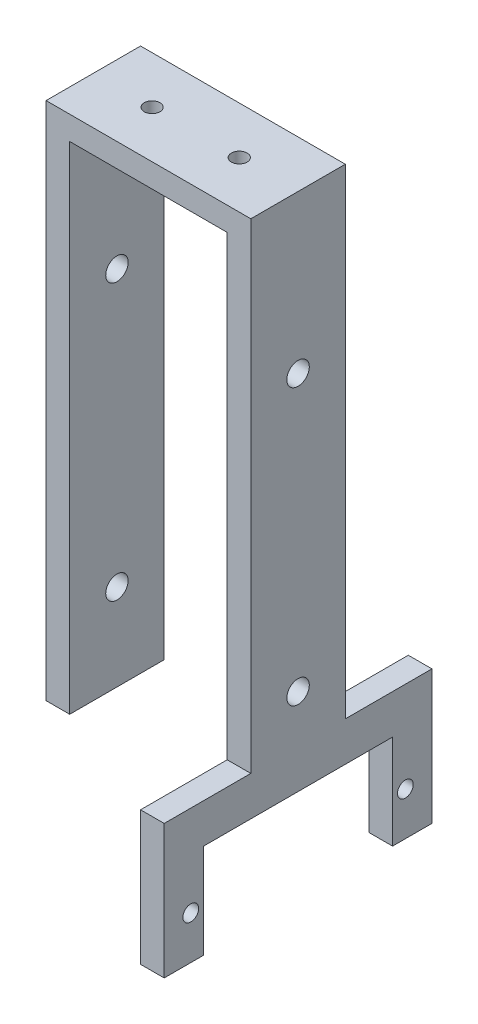
SolidWorks part; units mm, degrees
ref_plane "Front Plane" through (0, 0, 0) normal (0, 0, 1) x (1, 0, 0)
ref_plane "Top Plane" through (0, 0, 0) normal (0, 1, 0) x (1, 0, 0)
ref_plane "Right Plane" through (0, 0, 0) normal (1, 0, 0) x (0, 0, -1)
sketch "Sketch2" plane through (0, 0, 0) normal (0, 1, 0) x (1, 0, 0)
  line L1 (-13, -6) -> (13, -6)
  line L2 (-13, -6) -> (-13, 6)
  line L3 (-13, 6) -> (13, 6)
  line L4 (13, -6) -> (13, 6)
  line L5 (-13, -6) -> (13, 6) construction
  line L6 (-13, 6) -> (13, -6) construction
  point P0 (0, 0)
  dimension "D1" = 26
  dimension "D2" = 12
extrude "Boss-Extrude1" add sketch "Sketch2" along normal blind 3
sketch "Sketch3" plane through (0, 0, 0) normal (0, -1, 0) x (1, 0, 0)
  line L0 (-14.8214, 0) -> (17.6217, 0) construction
  line L1 (0, 14.1247) -> (0, -11.499) construction
  circle A0 centre (-5.535, 0) radius 1
  circle A1 centre (5.535, 0) radius 1
  dimension "D1" = 2
  dimension "D2" = 11.07
extrude "Cut-Extrude1" cut sketch "Sketch3" against normal blind 10
sketch "Sketch4" plane through (0, 0, 0) normal (0, -1, 0) x (1, 0, 0)
  line L0 (13, -6) -> (-13, -6) construction
  line L1 (-13, 6) -> (-10, 6)
  line L2 (-13, 6) -> (-13, -6)
  line L3 (-13, -6) -> (-10, -6)
  line L4 (-10, 6) -> (-10, -6)
  dimension "D1" = 3
extrude "Boss-Extrude2" add sketch "Sketch4" along normal blind 75
mirror "Mirror1" about plane through (0, 0, 0) normal (1, 0, 0) of "Boss-Extrude2"
sketch "Sketch5" plane through (-13, 0, 0) normal (-1, 0, 0) x (0, 0, 1)
  line L0 (0, -63.4205) -> (0, 21.0577) construction
  line L1 (-6, 3) -> (6, 3) construction
  circle A0 centre (0, -17) radius 1.425
  dimension "D1" = 2.85
  dimension "D2" = 20
extrude "Cut-Extrude2" cut sketch "Sketch5" against normal blind 30
pattern_linear "LPattern1" count 2 spacing 35 along (0, -1, 0) of "Cut-Extrude2"
sketch "Sketch6" plane through (13, 0, 0) normal (1, 0, 0) x (0, 0, -1)
  line L0 (-6, 3) -> (-6, -75) construction
  line L1 (-6, -58) -> (-17, -58)
  line L2 (-6, -58) -> (-6, -63)
  line L3 (-6, -63) -> (-12, -63)
  line L4 (-17, -58) -> (-17, -63)
  line L5 (-6, 3) -> (6, 3) construction
  line L7 (-17, -63) -> (-17, -75)
  line L8 (-17, -75) -> (-12, -75)
  line L9 (-12, -63) -> (-12, -75)
  point P9 (-11.5, -58)
  dimension "D1" = 12
  dimension "D2" = 5
  dimension "D3" = 61
  dimension "D4" = 5
  dimension "D5" = 5
  dimension "D6" = 6
extrude "Boss-Extrude3" add sketch "Sketch6" against normal blind 3
mirror "Mirror2" about plane through (0, 0, 0) normal (0, 0, 1) of "Boss-Extrude3"
sketch "Sketch7" plane through (13, 0, 0) normal (1, 0, 0) x (0, 0, -1)
  circle A0 centre (-13.625, -69.5263) radius 1
  dimension "D1" = 2
extrude "Cut-Extrude3" cut sketch "Sketch7" against normal blind 3
mirror "Mirror3" about plane through (0, 0, 0) normal (0, 0, 1) of "Cut-Extrude3"
sketch "Sketch8" plane through (13, 0, 0) normal (1, 0, 0) x (0, 0, -1)
  line L1 (6, -63) -> (-6, -63)
  line L2 (6, -63) -> (6, -75)
  line L3 (6, -75) -> (-6, -75)
  line L4 (-6, -63) -> (-6, -75)
extrude "Cut-Extrude4" cut sketch "Sketch8" against normal through all
